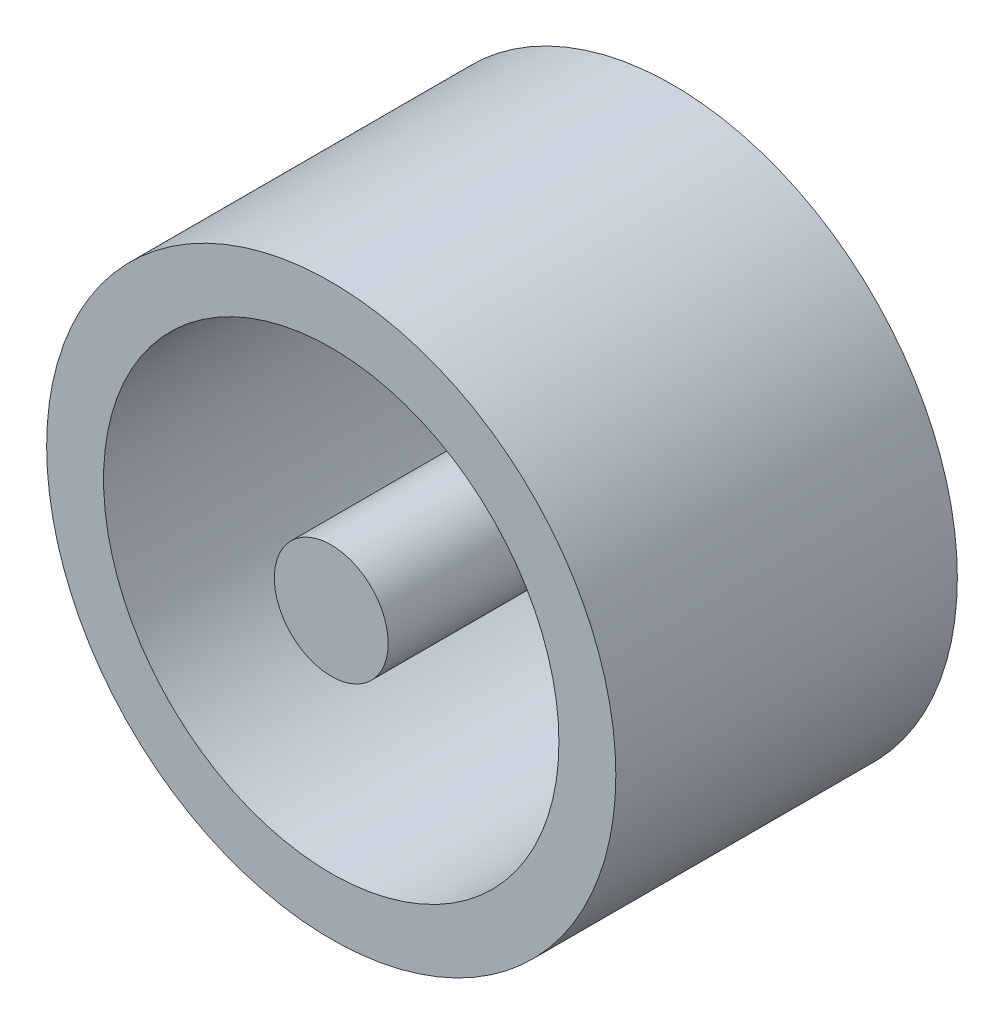
SolidWorks part; units mm, degrees
ref_plane "Plan de face" through (0, 0, 0) normal (0, 0, 1) x (1, 0, 0)
ref_plane "Plan de dessus" through (0, 0, 0) normal (0, 1, 0) x (1, 0, 0)
ref_plane "Plan de droite" through (0, 0, 0) normal (1, 0, 0) x (0, 0, -1)
sketch "Esquisse1" plane through (0, 0, 0) normal (0, 0, 1) x (1, 0, 0)
  circle A1 centre (0, 0) radius 1
  circle A2 centre (0, 0) radius 1.25
  dimension "D2" = 2
  dimension "D3" = 2.5
extrude "Boss.-Extru.1" add sketch "Esquisse1" along normal blind 1.5
sketch "Esquisse2" plane through (0, 0, 0) normal (0, 0, 1) x (1, 0, 0)
  circle A0 centre (0, 0) radius 0.25
  dimension "D1" = 0.5
extrude "Boss.-Extru.2" add sketch "Esquisse2" along normal blind 1.5 separate body
